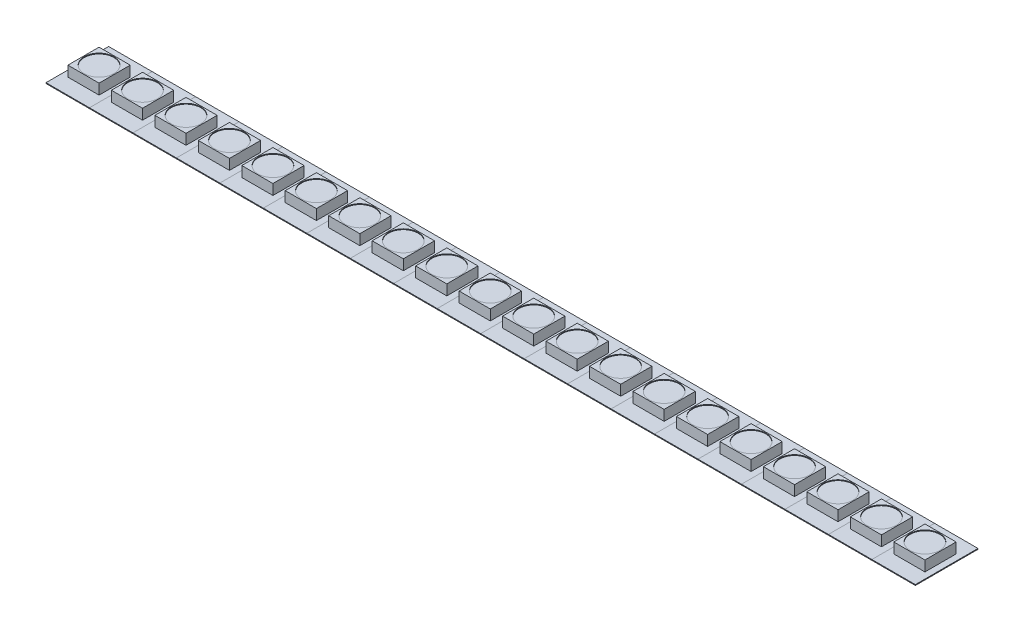
SolidWorks part; units mm, degrees
ref_plane "Front Plane" through (0, 0, 0) normal (0, 0, 1) x (1, 0, 0)
ref_plane "Top Plane" through (0, 0, 0) normal (0, 1, 0) x (1, 0, 0)
ref_plane "Right Plane" through (0, 0, 0) normal (1, 0, 0) x (0, 0, -1)
sketch "Sketch1" plane through (0, 0, 0) normal (0, 1, 0) x (1, 0, 0)
  line L0 (-3.4544, 4.9784) -> (3.4544, -4.9784) construction
  line L1 (-3.4544, 4.9784) -> (3.4544, 4.9784)
  line L2 (-3.4544, 4.9784) -> (-3.4544, -4.9784)
  line L3 (-3.4544, -4.9784) -> (3.4544, -4.9784)
  line L4 (3.4544, 4.9784) -> (3.4544, -4.9784)
  dimension "D1" = 9.9568
  dimension "D2" = 6.9088
extrude "Boss-Extrude1" add sketch "Sketch1" along normal blind 0.127
sketch "Sketch3" plane through (0, 0.127, 0) normal (0, 1, 0) x (1, 0, 0)
  line L0 (-3.4544, 4.9784) -> (3.4544, -4.9784) construction
  line L1 (-2.4765, 2.4765) -> (2.4765, -2.4765) construction
  line L2 (-2.4765, 2.4765) -> (2.4765, 2.4765)
  line L3 (-2.4765, 2.4765) -> (-2.4765, -2.4765)
  line L4 (-2.4765, -2.4765) -> (2.4765, -2.4765)
  line L5 (2.4765, 2.4765) -> (2.4765, -2.4765)
  dimension "D1" = 4.953
extrude "Boss-Extrude3" add sketch "Sketch3" along normal blind 1.651
sketch "Sketch5" plane through (0, 1.778, 0) normal (0, 1, 0) x (1, 0, 0)
  circle A0 centre (0, 0) radius 2.3483
extrude "Cut-Extrude1" cut sketch "Sketch5" against normal blind 0.127
pattern_linear "LPattern1" count 20 spacing 6.9088 along (1, 0, 0) of "Boss-Extrude3", "Cut-Extrude1", "Boss-Extrude1"
